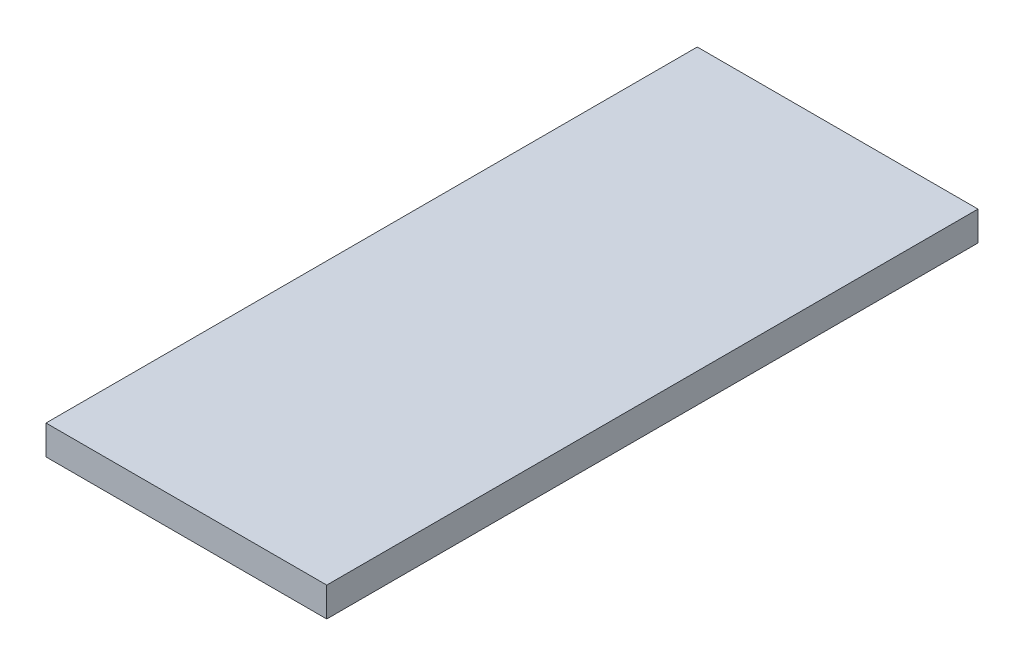
SolidWorks part; units mm, degrees
ref_plane "Front Plane" through (0, 0, 0) normal (0, 0, 1) x (1, 0, 0)
ref_plane "Top Plane" through (0, 0, 0) normal (0, 1, 0) x (1, 0, 0)
ref_plane "Right Plane" through (0, 0, 0) normal (1, 0, 0) x (0, 0, -1)
sketch "Sketch1" plane through (0, 0, 0) normal (0, 1, 0) x (1, 0, 0)
  line L1 (0, 0) -> (24.257, 0)
  line L2 (0, 0) -> (0, 56.2737)
  line L3 (0, 56.2737) -> (24.257, 56.2737)
  line L4 (24.257, 0) -> (24.257, 56.2737)
  dimension "D1" = 56.2737
  dimension "D2" = 24.257
extrude "Boss-Extrude1" add sketch "Sketch1" along normal blind 2.54
